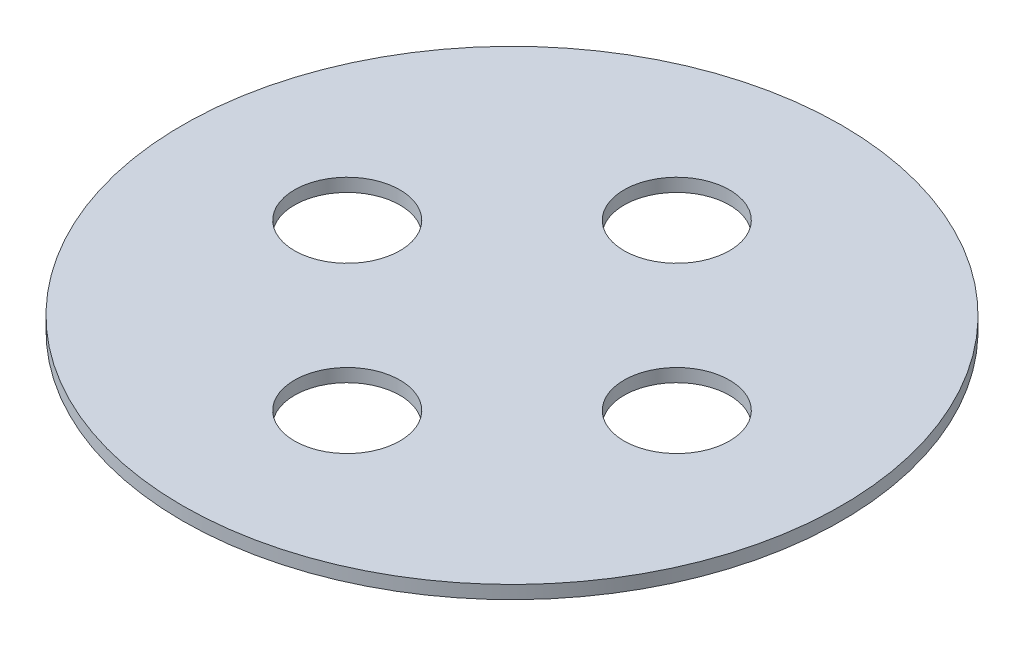
SolidWorks part; units mm, degrees
ref_plane "Front Plane" through (0, 0, 0) normal (0, 0, 1) x (1, 0, 0)
ref_plane "Top Plane" through (0, 0, 0) normal (0, 1, 0) x (1, 0, 0)
ref_plane "Right Plane" through (0, 0, 0) normal (1, 0, 0) x (0, 0, -1)
sketch "Sketch1" plane through (0, 0, 0) normal (0, 1, 0) x (1, 0, 0)
  circle A0 centre (0, 0) radius 25
  dimension "D1" = 50
extrude "Boss-Extrude1" add sketch "Sketch1" along normal blind 1
sketch "Sketch2" plane through (0, 1, 0) normal (0, 1, 0) x (1, 0, 0)
  line L0 (0, 0) -> (25, 0) construction
  line L1 (0, 0) -> (-25, 0) construction
  line L2 (0, 0) -> (0, 25) construction
  line L3 (0, 0) -> (0, -25) construction
  circle A0 centre (0, 0) radius 25 construction
  circle A1 centre (0, 12.5) radius 4
  circle A2 centre (12.5, 0) radius 4
  circle A3 centre (-12.5, 0) radius 4
  circle A4 centre (0, -12.5) radius 4
  dimension "D1" = 8
  dimension "D3" = 8
  dimension "D4" = 8
  dimension "D5" = 8
  dimension "D2" = 12.5
extrude "Cut-Extrude1" cut sketch "Sketch2" against normal blind 1
